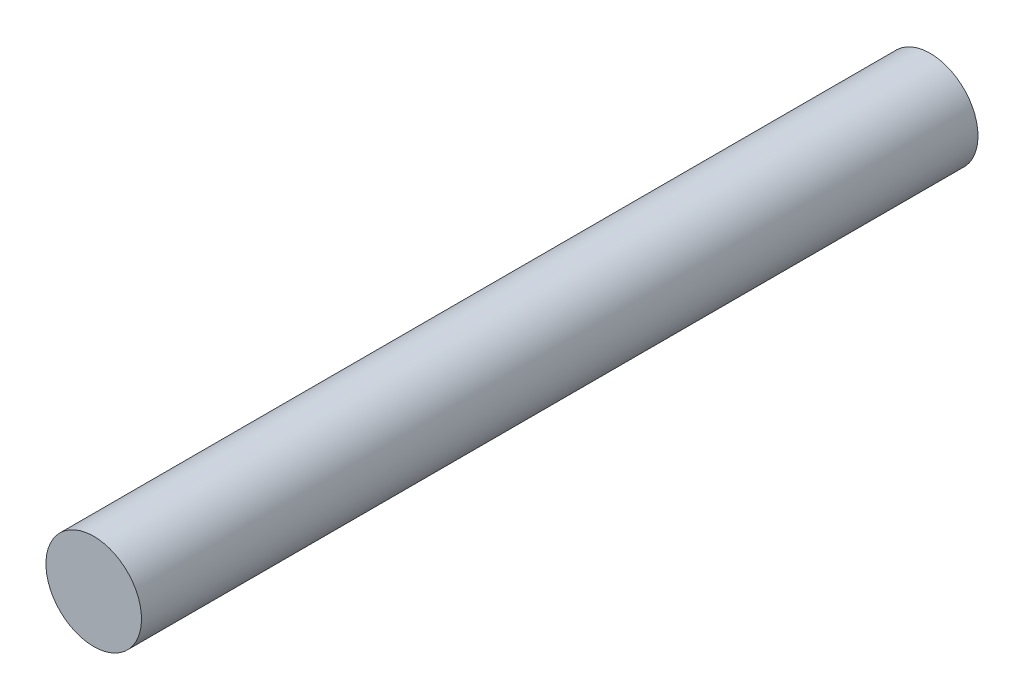
SolidWorks part; units mm, degrees
material "AISI 304"
ref_plane "Front Plane" through (0, 0, 0) normal (0, 0, 1) x (1, 0, 0)
ref_plane "Top Plane" through (0, 0, 0) normal (0, 1, 0) x (1, 0, 0)
ref_plane "Right Plane" through (0, 0, 0) normal (1, 0, 0) x (0, 0, -1)
sketch "Sketch1" plane through (0, 0, 0) normal (0, 0, 1) x (1, 0, 0)
  circle A0 centre (0, 0) radius 2
  dimension "D1" = 4
extrude "Boss-Extrude1" add sketch "Sketch1" along normal blind 35
